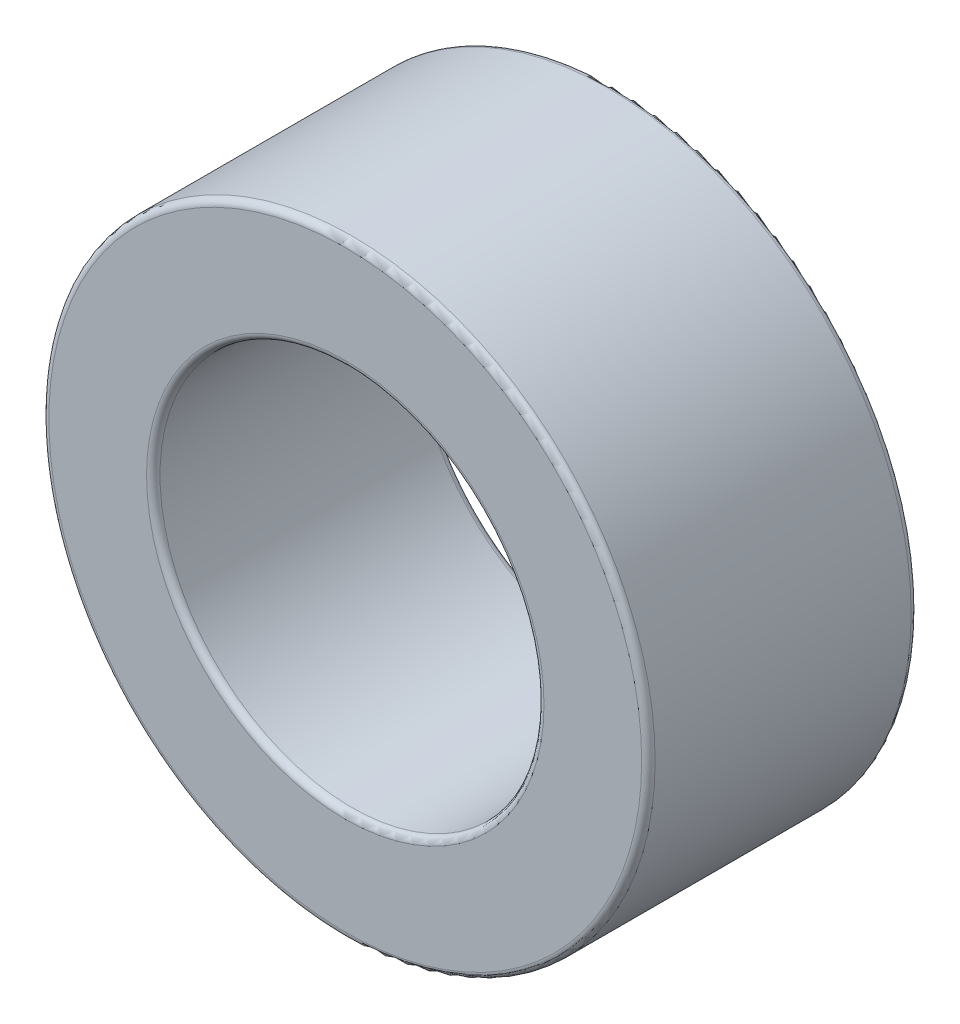
SolidWorks part; units mm, degrees
ref_plane "Front" through (0, 0, 0) normal (0, 0, 1) x (1, 0, 0)
ref_plane "Top" through (0, 0, 0) normal (0, 1, 0) x (1, 0, 0)
ref_plane "Right" through (0, 0, 0) normal (1, 0, 0) x (0, 0, -1)
sketch "草图1" plane through (0, 0, 0) normal (0, 0, 1) x (1, 0, 0)
  circle A0 centre (0, 0) radius 2.85
  circle A1 centre (0, 0) radius 4.5
  dimension "D1" = 5.7
  dimension "D2" = 9
extrude "凸台-拉伸1" add sketch "草图1" along normal blind 4
fillet "圆角1" radius 0.1 4 edges at (2.85, 0, 4) (2.85, 0, 0) (4.5, 0, 0) (4.5, 0, 4)
